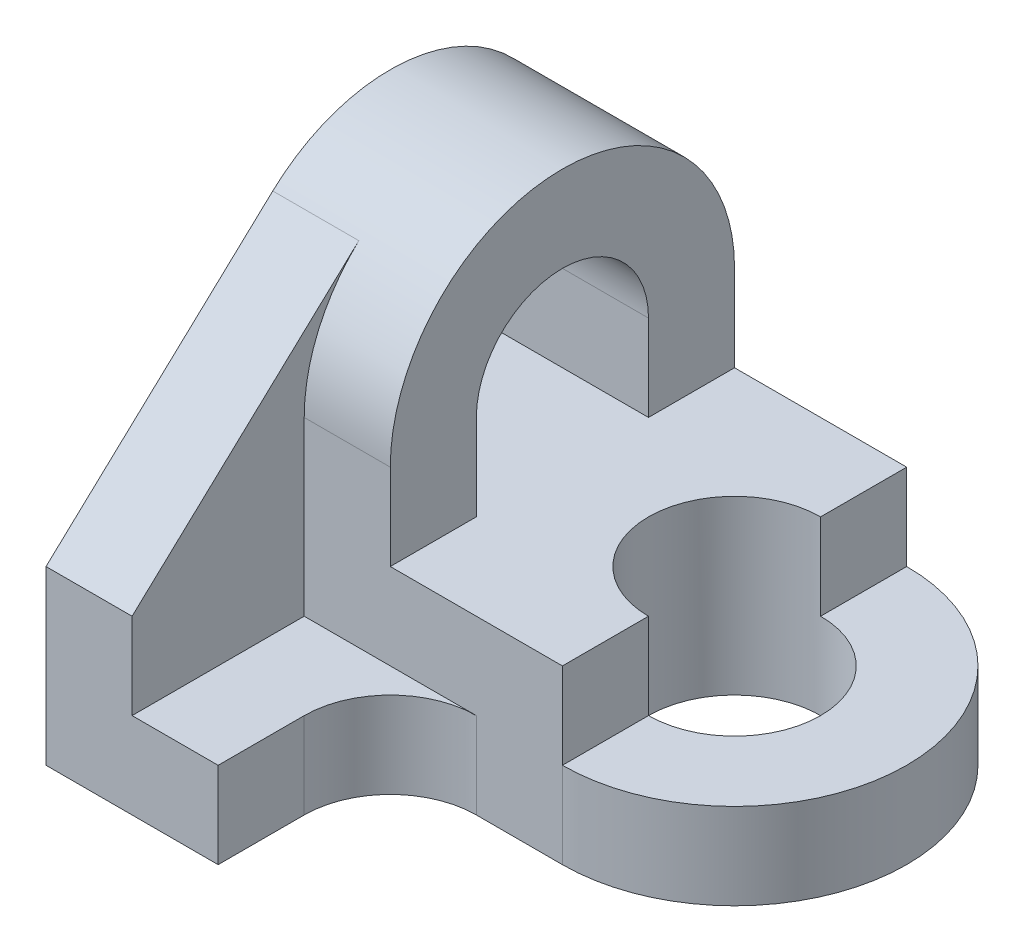
SolidWorks part; units mm, degrees
ref_plane "Front Plane" through (0, 0, 0) normal (0, 0, 1) x (1, 0, 0)
ref_plane "Top Plane" through (0, 0, 0) normal (0, 1, 0) x (1, 0, 0)
ref_plane "Right Plane" through (0, 0, 0) normal (1, 0, 0) x (0, 0, -1)
sketch "Sketch1" plane through (0, 0, 0) normal (0, 0, 1) x (1, 0, 0)
  line L1 (-2, -1) -> (2, -1)
  line L2 (-2, -1) -> (-2, 1)
  line L3 (-2, 1) -> (2, 1)
  line L4 (2, -1) -> (2, 1)
  line L5 (-2, -1) -> (2, 1) construction
  line L6 (-2, 1) -> (2, -1) construction
  point P0 (0, 0)
  dimension "D1" = 4
  dimension "D2" = 2
extrude "Boss-Extrude1" add sketch "Sketch1" along normal blind 4
sketch "Sketch2" plane through (0, -1, 0) normal (0, -1, 0) x (1, 0, 0)
  line L0 (2, 4) -> (2, 0)
  arc A0 (2, 4) -> (2, 0) centre (2, 2) cw
  dimension "D1" = 2
extrude "Boss-Extrude2" add sketch "Sketch2" against normal blind 1
sketch "Sketch3" plane through (0, 1, 0) normal (0, 1, 0) x (1, 0, 0)
  line L0 (2, -4) -> (2, 0) construction
  circle A0 centre (2, -2) radius 1
  dimension "D1" = 2
extrude "Cut-Extrude1" cut sketch "Sketch3" against normal through all
sketch "Sketch4" plane through (-2, 0, 0) normal (-1, 0, 0) x (0, 0, 1)
  line L0 (4, 0) -> (4, -1)
  line L1 (4, -1) -> (6, -1)
  line L2 (6, -1) -> (6, 0)
  line L3 (6, 0) -> (4, 0)
  line L4 (0, 1) -> (0, 2)
  line L5 (4, 1) -> (4, 2)
  line L6 (1, 1) -> (1, 2)
  line L7 (3, 1) -> (3, 2)
  line L8 (1, 1) -> (0, 1)
  line L9 (3, 1) -> (4, 1)
  arc A0 (0, 2) -> (4, 2) centre (2, 2) cw
  arc A1 (1, 2) -> (3, 2) centre (2, 2) cw
  dimension "D1" = 1
  dimension "D2" = 1
  dimension "D3" = 2
  dimension "D4" = 1
  dimension "D5" = 1
extrude "Boss-Extrude3" add sketch "Sketch4" against normal blind 2
sketch "Sketch5" plane through (0, 0, 0) normal (0, 1, 0) x (1, 0, 0)
  line L0 (-1, -6) -> (-2, -6)
  line L1 (0, -6) -> (-2, -6) construction
  line L2 (-2, -6) -> (-2, -4)
  line L3 (-2, -4) -> (-1, -4)
  line L4 (-1, -4) -> (-1, -6)
extrude "Boss-Extrude4" add sketch "Sketch5" along normal blind 1
sketch "Sketch6" plane through (-2, 0, 0) normal (-1, 0, 0) x (0, 0, 1)
  line L0 (3.3654, 3.4614) -> (6, 1)
  line L1 (6, 1) -> (4, 1)
  line L2 (4, 1) -> (4, 2)
  arc A0 (4, 2) -> (0, 2) centre (2, 2) ccw construction
  arc A1 (3.3654, 3.4614) -> (4, 2) centre (2, 2) cw
extrude "Boss-Extrude5" add sketch "Sketch6" against normal blind 1
sketch "Sketch7" plane through (0, 0, 0) normal (0, 1, 0) x (1, 0, 0)
  line L0 (2, -4) -> (0, -4) construction
  line L1 (0, -6) -> (0, -4) construction
  line L2 (1, -4) -> (0, -4)
  line L3 (0, -4) -> (0, -5)
  arc A0 (1, -4) -> (0, -5) centre (1, -5) ccw
extrude "Boss-Extrude6" add sketch "Sketch7" against normal blind 1
